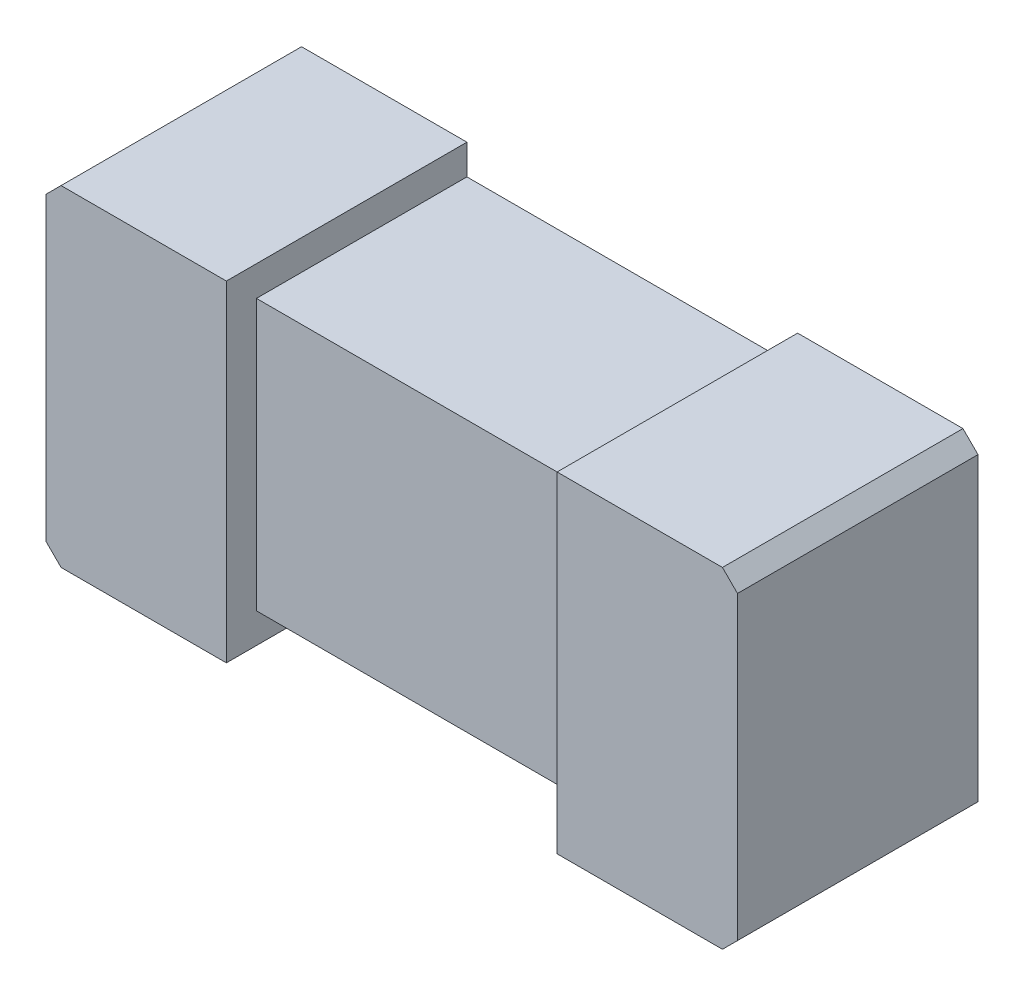
SolidWorks part; units mm, degrees
ref_plane "Front" through (0, 0, 0) normal (0, 0, 1) x (1, 0, 0)
ref_plane "Top" through (0, 0, 0) normal (0, 1, 0) x (1, 0, 0)
ref_plane "Right" through (0, 0, 0) normal (1, 0, 0) x (0, 0, -1)
sketch "COMPONENT_OUTLINE" plane through (0, 0, 0) normal (0, 0, 1) x (1, 0, 0)
  line L0 (0.55, 0.275) -> (-0.55, 0.275)
  line L1 (-0.55, 0.275) -> (-0.575, 0.25)
  line L2 (-0.575, 0.25) -> (-0.575, -0.25)
  line L3 (-0.575, -0.25) -> (-0.55, -0.275)
  line L4 (-0.55, -0.275) -> (0.55, -0.275)
  line L5 (0.55, -0.275) -> (0.575, -0.25)
  line L6 (0.575, -0.25) -> (0.575, 0.25)
  line L7 (0.575, 0.25) -> (0.55, 0.275)
extrude "Extrude1" add sketch "COMPONENT_OUTLINE" along normal blind 0.4
sketch "Sketch1" plane through (0, 0, 0.4) normal (0, 0, 1) x (1, 0, 0)
  line L8 (-0.275, 0.275) -> (-0.275, 0.225)
  line L9 (0.275, -0.275) -> (0.275, -0.225)
  line L10 (0.275, 0.225) -> (0.275, 0.275)
  line L11 (-0.275, -0.225) -> (-0.275, -0.275)
  line L16 (0.525, 0.225) -> (-0.525, 0.225)
  line L17 (-0.525, 0.225) -> (-0.525, -0.225)
  line L18 (-0.525, -0.225) -> (0.525, -0.225)
  line L19 (0.525, -0.225) -> (0.525, 0.225)
  line L20 (0.275, 0.225) -> (-0.275, 0.225)
  line L22 (-0.275, -0.225) -> (0.275, -0.225)
  line L24 (0.575, 0.25) -> (0.55, 0.275)
  line L25 (0.55, 0.275) -> (-0.55, 0.275)
  line L26 (-0.55, 0.275) -> (-0.575, 0.25)
  line L27 (-0.575, 0.25) -> (-0.575, -0.25)
  line L28 (-0.575, -0.25) -> (-0.55, -0.275)
  line L29 (-0.55, -0.275) -> (0.55, -0.275)
  line L30 (0.55, -0.275) -> (0.575, -0.25)
  line L31 (0.575, -0.25) -> (0.575, 0.25)
  line L33 (0.275, 0.275) -> (-0.275, 0.275)
  line L37 (-0.275, -0.275) -> (0.275, -0.275)
  dimension "D1" = 0.05
  dimension "D2" = 0
extrude "Cut-Extrude1" cut sketch "Sketch1" against normal through all
sketch "Sketch2" plane through (0, -0.225, 0) normal (0, -1, 0) x (1, 0, 0)
  line L0 (0.275, 0.35) -> (-0.275, 0.35)
  line L4 (0.275, 0.4) -> (-0.275, 0.4)
  line L5 (-0.275, 0.4) -> (-0.275, 0)
  line L6 (-0.275, 0) -> (0.275, 0)
  line L7 (0.275, 0) -> (0.275, 0.4)
  line L8 (0.275, 0.4) -> (-0.275, 0.4)
  line L9 (-0.275, 0.4) -> (-0.275, 0.35)
  line L11 (0.275, 0.35) -> (0.275, 0.4)
  dimension "D1" = 0
  dimension "D2" = 0.05
extrude "Cut-Extrude2" cut sketch "Sketch2" against normal blind 5
